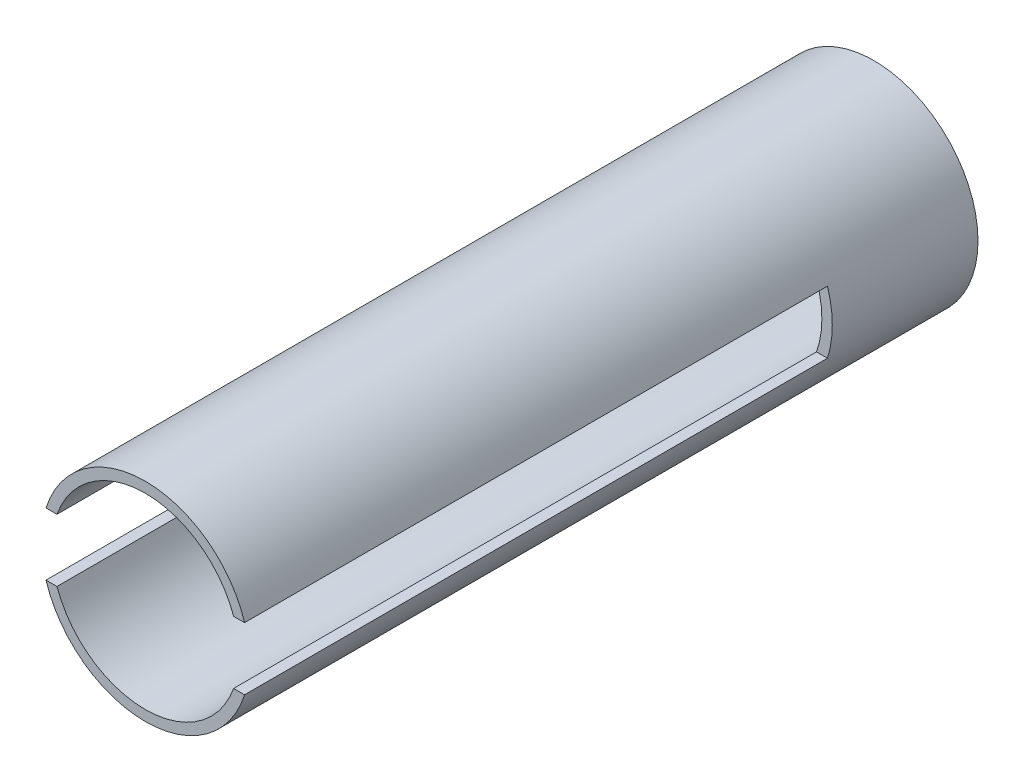
SolidWorks part; units mm, degrees
ref_plane "Front Plane" through (0, 0, 0) normal (0, 0, 1) x (1, 0, 0)
ref_plane "Top Plane" through (0, 0, 0) normal (0, 1, 0) x (1, 0, 0)
ref_plane "Right Plane" through (0, 0, 0) normal (1, 0, 0) x (0, 0, -1)
sketch "Sketch1" plane through (0, 0, 0) normal (0, 0, 1) x (1, 0, 0)
  line L1 (-88.9, -19.05) -> (88.9, -19.05)
  line L2 (-88.9, -19.05) -> (-88.9, 19.05) construction
  line L3 (-88.9, 19.05) -> (88.9, 19.05)
  line L4 (88.9, -19.05) -> (88.9, 19.05) construction
  line L5 (-88.9, -19.05) -> (88.9, 19.05) construction
  line L6 (-88.9, 19.05) -> (88.9, -19.05) construction
  circle A0 centre (0, 0) radius 63.5
  circle A1 centre (0, 0) radius 57.15
  dimension "D1" = 127
  dimension "D4" = 6.35
  dimension "D2" = 38.1
  dimension "D3" = 177.8
extrude "Boss-Extrude1" add sketch "Sketch1" along normal mid plane 355.6 contours A1 L3 A0 | A1 L1 A0
sketch "Sketch2" plane through (0, 0, -177.8) normal (0, 0, -1) x (-1, 0, 0)
  circle A0 centre (0, 0) radius 63.5 construction
  circle A1 centre (0, 0) radius 57.15 construction
  circle A2 centre (0, 0) radius 63.5
  circle A3 centre (0, 0) radius 57.15
extrude "Boss-Extrude2" add sketch "Sketch2" along normal blind 88.9
